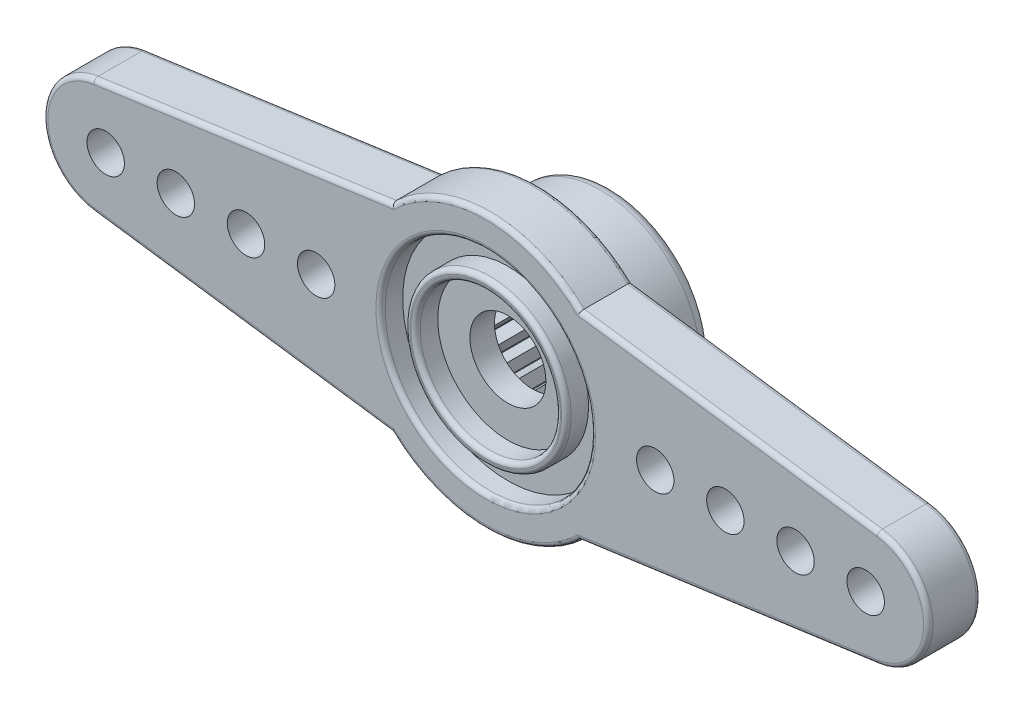
SolidWorks part; units mm, degrees
material "PEI"
ref_plane "Front Plane" through (0, 0, 0) normal (0, 0, 1) x (1, 0, 0)
ref_plane "Top Plane" through (0, 0, 0) normal (0, 1, 0) x (1, 0, 0)
ref_plane "Right Plane" through (0, 0, 0) normal (1, 0, 0) x (0, 0, -1)
sketch "Эскиз1" plane through (0, 0, 0) normal (0, 0, 1) x (1, 0, 0)
  circle A0 centre (0, 0) radius 4.3
  dimension "D1" = 8.6
extrude "Бобышка-Вытянуть1" add sketch "Эскиз1" along normal mid plane 5.4
sketch "Эскиз2" plane through (0, 0, 2.7) normal (0, 0, 1) x (1, 0, 0)
  line L0 (0, -1000) -> (0, 49000) construction
  line L1 (-1000, 0) -> (49000, 0) construction
  line L2 (-16.7695, 2.4761) -> (-4.02, 4.25)
  line L3 (-16.7695, -2.4761) -> (-4.02, -4.25)
  line L4 (4.02, 4.25) -> (16.7695, 2.4761)
  line L5 (4.02, -4.25) -> (16.7695, -2.4761)
  arc A0 (-4.02, -4.25) -> (4.02, -4.25) centre (0, 0) ccw
  arc A1 (-16.7695, 2.4761) -> (-16.7695, -2.4761) centre (-16.425, 0) ccw
  arc A2 (16.7695, -2.4761) -> (16.7695, 2.4761) centre (16.425, 0) ccw
  arc A3 (4.02, 4.25) -> (-4.02, 4.25) centre (0, 0) ccw
  dimension "D1" = 11.7
  dimension "D2" = 37.85
  dimension "D3" = 5
  dimension "D4" = 8.5
extrude "Бобышка-Вытянуть2" add sketch "Эскиз2" against normal blind 2.25
sketch "Эскиз3" plane through (0, 0, 2.7) normal (0, 0, 1) x (1, 0, 0)
  circle A0 centre (0, 0) radius 4.5
  circle A1 centre (0, 0) radius 3.45
  circle A2 centre (0, 0) radius 3
  dimension "D1" = 9
  dimension "D2" = 6.9
  dimension "D3" = 6
extrude "Вырез-Вытянуть1" cut sketch "Эскиз3" against normal blind 0.95 contours A2 | A0 A1
fillet "Скругление1" radius 0.2 20 edges at (-10.3947, -3.3631, 0.45) (0, -5.85, 0.45) (10.3947, -3.3631, 0.45) (18.925, 0, 0.45) (10.3947, 3.3631, 0.45) (0, 5.85, 0.45) (-10.3947, 3.3631, 0.45) (-18.925, 0, 0.45) (4.3, 0, 0.45) (-10.3947, 3.3631, 2.7) (0, 5.85, 2.7) (10.3947, 3.3631, 2.7) (18.925, 0, 2.7) (10.3947, -3.3631, 2.7) (0, -5.85, 2.7) (-10.3947, -3.3631, 2.7) (-18.925, 0, 2.7) (4.5, 0, 2.7) (3.45, 0, 2.7) (3, 0, 2.7)
fillet "Скругление2" radius 0.5 1 edges at (4.3, 0, -2.7)
sketch "Эскиз4" plane through (0, 0, 1.75) normal (0, 0, 1) x (1, 0, 0)
  circle A0 centre (0, 0) radius 1.625
  dimension "D1" = 3.25
extrude "Вырез-Вытянуть2" cut sketch "Эскиз4" against normal through all
sketch "Эскиз5" plane through (0, 0, -2.7) normal (0, 0, -1) x (-1, 0, 0)
  circle A0 centre (0, 0) radius 2.9
  dimension "D1" = 5.8
extrude "Вырез-Вытянуть3" cut sketch "Эскиз5" against normal blind 3.4
sketch "Эскиз8" plane through (0, 0, -2.7) normal (0, 0, -1) x (-1, 0, 0)
  line L0 (0, -1000) -> (0, 49000) construction
  line L3 (0.35, -2.8788) -> (0, -2.4)
  line L4 (0, -2.4) -> (-0.35, -2.8788)
  circle A5 centre (0, 0) radius 2.9
  arc A6 (-0.35, -2.8788) -> (0.35, -2.8788) centre (0, 0) ccw
  dimension "D1" = 0
  dimension "D2" = 0.7
  dimension "D3" = 0.5
extrude "Бобышка-Вытянуть3" add sketch "Эскиз8" against normal up to surface (3.4 mm away) up to face at (-2.9, 0, 0.7)
pattern_circular "Круговой массив1" count 25 over 360 about axis through (0, 0, 0) along (0, 0, 1) of "Бобышка-Вытянуть3"
sketch "Эскиз9" plane through (0, 0, 2.7) normal (0, 0, 1) x (1, 0, 0)
  line L0 (0, -1000) -> (0, 49000) construction
  circle A0 centre (7.25, 0) radius 0.8
  circle A1 centre (10.25, 0) radius 0.8
  circle A2 centre (13.25, 0) radius 0.8
  circle A3 centre (16.25, 0) radius 0.8
  dimension "D1" = 14.5
  dimension "D2" = 1.6
  dimension "D4" = 3
  dimension "D3" = 4
extrude "Вырез-Вытянуть7" cut sketch "Эскиз9" against normal up to surface (2.25 mm away) up to face at (0, 0, 0.45)
mirror "Зеркальное отражение1" about plane through (0, 0, 0) normal (1, 0, 0) of "Вырез-Вытянуть7"
